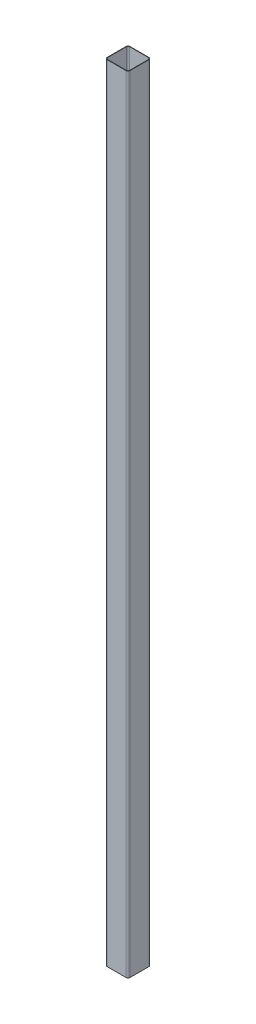
SolidWorks part; units mm, degrees
ref_plane "Front Plane" through (0, 0, 0) normal (0, 0, 1) x (1, 0, 0)
ref_plane "Top Plane" through (0, 0, 0) normal (0, 1, 0) x (1, 0, 0)
ref_plane "Right Plane" through (0, 0, 0) normal (1, 0, 0) x (0, 0, -1)
sketch "Sketch1" plane through (0, 0, 0) normal (0, 1, 0) x (1, 0, 0)
  line L0 (14.605, 17.145) -> (-14.605, 17.145)
  line L1 (14.605, -17.78) -> (-14.605, -17.78)
  line L2 (17.78, -14.605) -> (17.78, 14.605)
  line L3 (14.605, 17.78) -> (-14.605, 17.78)
  line L4 (-17.78, -14.605) -> (-17.78, 14.605)
  line L5 (17.78, -17.78) -> (-17.78, 17.78) construction
  line L6 (17.78, 17.78) -> (-17.78, -17.78) construction
  line L7 (-17.145, -14.605) -> (-17.145, 14.605)
  line L8 (14.605, -17.145) -> (-14.605, -17.145)
  line L9 (17.145, -14.605) -> (17.145, 14.605)
  arc A0 (-17.78, -14.605) -> (-14.605, -17.78) centre (-14.605, -14.605) ccw
  arc A1 (14.605, -17.78) -> (17.78, -14.605) centre (14.605, -14.605) ccw
  arc A2 (17.78, 14.605) -> (14.605, 17.78) centre (14.605, 14.605) ccw
  arc A3 (-14.605, 17.78) -> (-17.78, 14.605) centre (-14.605, 14.605) ccw
  arc A4 (-14.605, 17.145) -> (-17.145, 14.605) centre (-14.605, 14.605) ccw
  arc A5 (-17.145, -14.605) -> (-14.605, -17.145) centre (-14.605, -14.605) ccw
  arc A6 (14.605, -17.145) -> (17.145, -14.605) centre (14.605, -14.605) ccw
  arc A7 (17.145, 14.605) -> (14.605, 17.145) centre (14.605, 14.605) ccw
  point P0 (0, 0)
  dimension "D2" = 3.175
  dimension "D3" = 3.175
  dimension "D4" = 3.175
  dimension "D5" = 3.175
  dimension "D1" = 35.56
  dimension "D6" = 0.635
extrude "Boss-Extrude1" add sketch "Sketch1" along normal blind 1219.2
